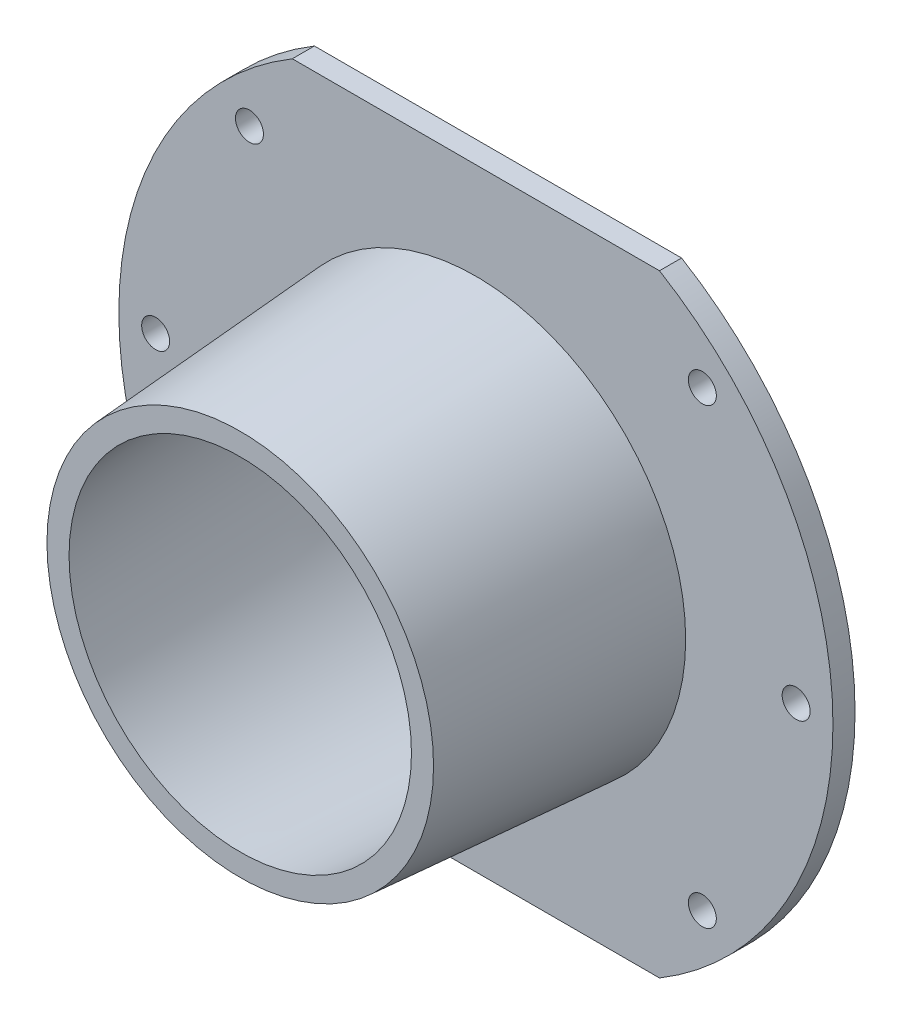
SolidWorks part; units mm, degrees
ref_plane "Front Plane" through (0, 0, 0) normal (0, 0, 1) x (1, 0, 0)
ref_plane "Top Plane" through (0, 0, 0) normal (0, 1, 0) x (1, 0, 0)
ref_plane "Right Plane" through (0, 0, 0) normal (1, 0, 0) x (0, 0, -1)
sketch "Sketch1" plane through (0, 0, 0) normal (0, 0, 1) x (1, 0, 0)
  circle A0 centre (0, 0) radius 23.25
  circle A1 centre (0, 0) radius 26.25
  dimension "D1" = 46.5
  dimension "D2" = 3
sketch "Sketch2" plane through (0, 0, 0) normal (0, 1, 0) x (1, 0, 0)
  line L0 (-23.25, 0) -> (-25.6974, 35)
  line L1 (-25.6974, 35) -> (-28.6974, 35)
  line L2 (-28.6974, 35) -> (-26.25, 0)
  line L3 (-26.25, 0) -> (-23.25, 0)
  line L4 (-23.25, 0) -> (-23.25, 35) construction
  line L5 (-23.25, 35) -> (-25.6974, 35) construction
  line L6 (-23.25, 0) -> (23.25, 0) construction
  line L9 (0, 0) -> (0, 35) construction
  line L10 (0, 35) -> (-23.25, 35) construction
  line L11 (-28.6974, 35) -> (-48.4877, 35)
  line L12 (-48.4877, 35) -> (-48.4877, 32)
  line L13 (-48.4877, 32) -> (-28.4877, 32)
  dimension "D1" = 4
  dimension "D2" = 35
  dimension "D3" = 3
  dimension "D4" = 20
revolve "Revolve1" add sketch "Sketch2" angle 360 about L9
sketch "Sketch3" plane through (0, 0, -32) normal (0, 0, 1) x (1, 0, 0)
  line L0 (0, 0) -> (28.4877, 0) construction
  line L1 (28.4877, 0) -> (48.4877, 0) construction
  circle A0 centre (0, 0) radius 28.4877 construction
  circle A1 centre (0, 0) radius 48.4877 construction
  circle A2 centre (43.4877, 0) radius 1.9
  dimension "D1" = 3.8
  dimension "D2" = 5
extrude "Cut-Extrude1" cut sketch "Sketch3" against normal through all
pattern_circular "CirPattern1" count 8 over 360 about axis through (0, 0, 0) along (0, 0, 1) of "Cut-Extrude1"
sketch "Sketch4" plane through (0, 0, -32) normal (0, 0, 1) x (1, 0, 0)
  line L0 (-48.4877, 0) -> (-28.4877, 0) construction
  line L1 (-48.4877, -41.5877) -> (48.4877, -41.5877)
  line L2 (-48.4877, -41.5877) -> (-48.4877, 41.5877)
  line L3 (-48.4877, 41.5877) -> (48.4877, 41.5877)
  line L4 (48.4877, -41.5877) -> (48.4877, 41.5877)
  line L5 (-48.4877, -41.5877) -> (48.4877, 41.5877) construction
  line L6 (-48.4877, 41.5877) -> (48.4877, -41.5877) construction
  line L11 (-98.4877, -91.5877) -> (-98.4877, 91.5877)
  line L12 (-98.4877, 91.5877) -> (98.4877, 91.5877)
  line L13 (0, 43.4877) -> (0, 41.5877) construction
  line L14 (98.4877, -91.5877) -> (98.4877, 91.5877)
  line L15 (-98.4877, -91.5877) -> (98.4877, -91.5877)
  circle A0 centre (0, 43.4877) radius 1.9 construction
  circle A1 centre (0, 0) radius 48.4877 construction
  point P0 (0, 0)
  point P6 (0, 0)
  point P11 (0, 41.5877)
  point P15 (-48.4877, 0)
  dimension "D1" = 50
extrude "Cut-Extrude2" cut sketch "Sketch4" against normal through all
